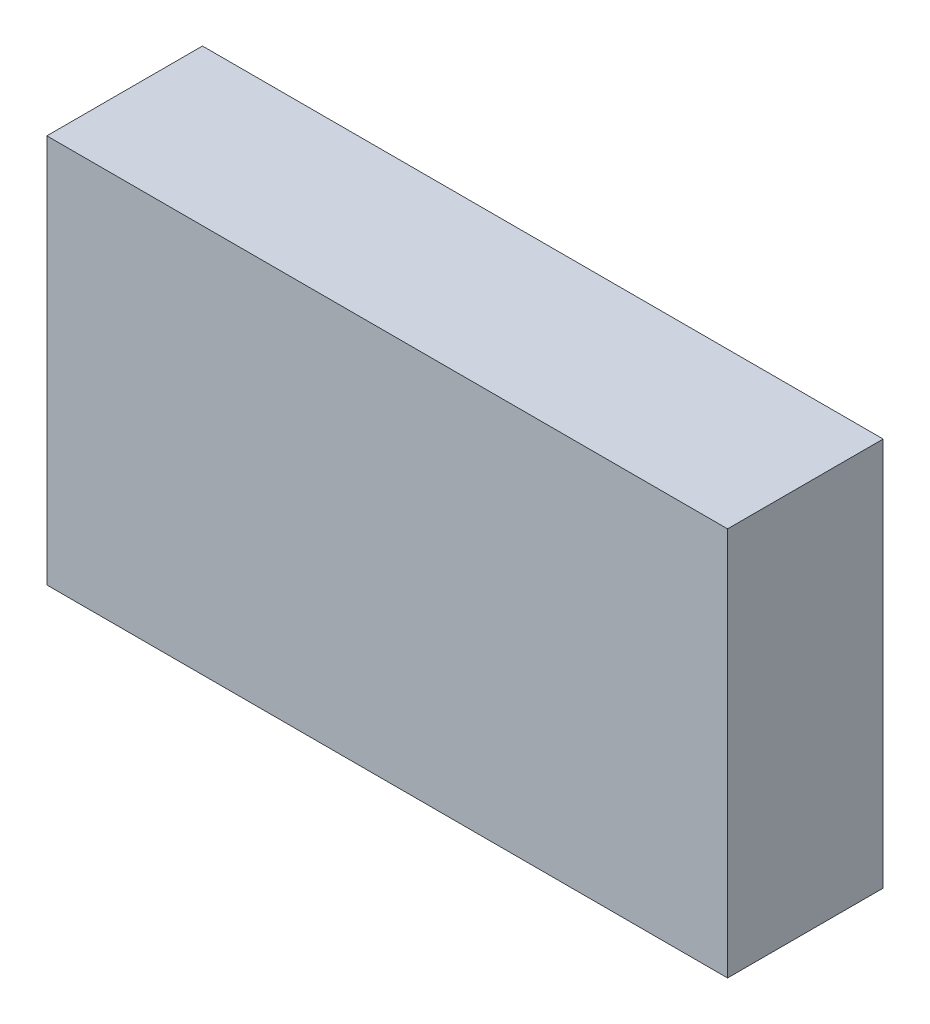
SolidWorks part; units mm, degrees
material "BUTYL"
ref_plane "Plano frontal" through (0, 0, 0) normal (0, 0, 1) x (1, 0, 0)
ref_plane "Plano superior" through (0, 0, 0) normal (0, 1, 0) x (1, 0, 0)
ref_plane "Plano direito" through (0, 0, 0) normal (1, 0, 0) x (0, 0, -1)
sketch "Esboço1" plane through (0, 0, 0) normal (0, 0, 1) x (1, 0, 0)
  line L1 (-17.5, 10) -> (17.5, 10)
  line L2 (-17.5, 10) -> (-17.5, -10)
  line L3 (-17.5, -10) -> (17.5, -10)
  line L4 (17.5, 10) -> (17.5, -10)
  line L5 (-17.5, 10) -> (17.5, -10) construction
  line L6 (-17.5, -10) -> (17.5, 10) construction
  point P0 (0, 0)
  dimension "D1" = 20
  dimension "D2" = 35
extrude "Ressalto-extrusão1" add sketch "Esboço1" along normal blind 8
